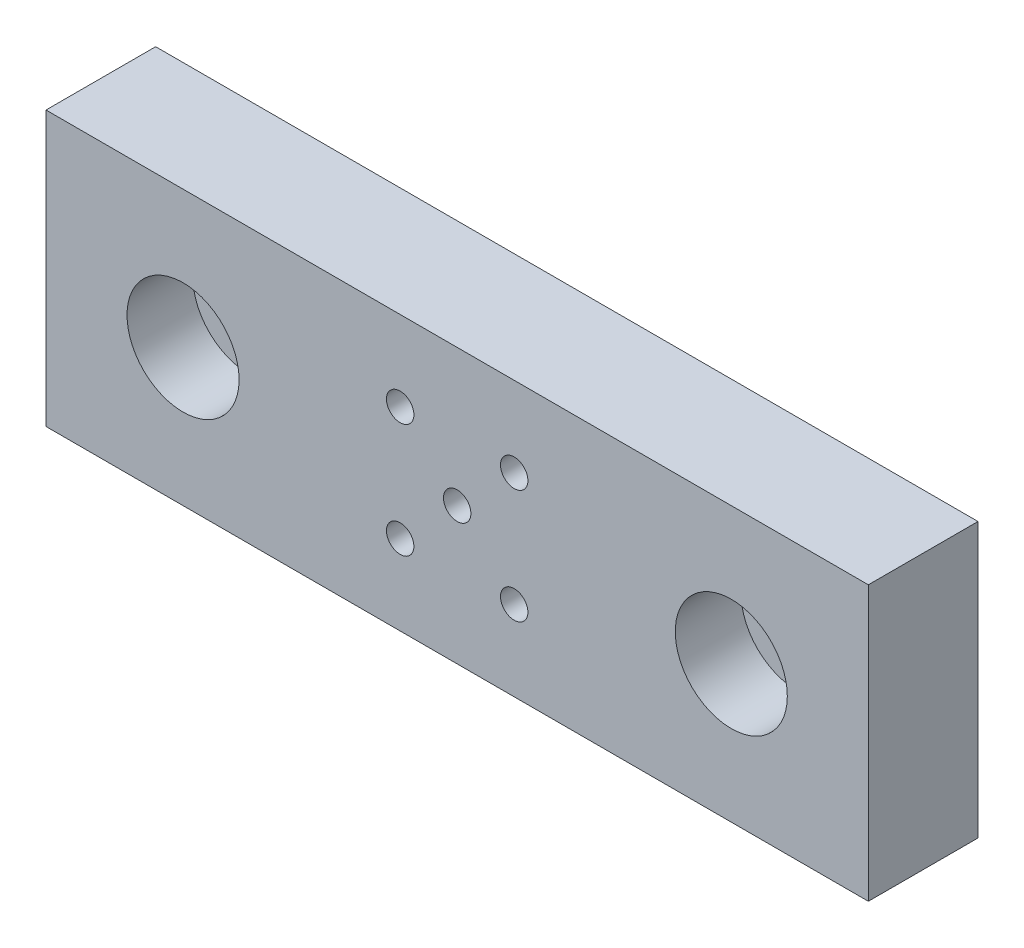
SolidWorks part; units mm, degrees
ref_plane "Front Plane" through (0, 0, 0) normal (0, 0, 1) x (1, 0, 0)
ref_plane "Top Plane" through (0, 0, 0) normal (0, 1, 0) x (1, 0, 0)
ref_plane "Right Plane" through (0, 0, 0) normal (1, 0, 0) x (0, 0, -1)
sketch "Sketch1" plane through (0, 0, 0) normal (0, 0, 1) x (1, 0, 0)
  line L0 (-48.6207, 0) -> (72.931, 0) construction
  line L1 (0, 34.4847) -> (0, -34.4847) construction
  line L2 (-37.5, 12.5) -> (37.5, 12.5)
  line L3 (-37.5, -12.5) -> (37.5, -12.5)
  line L4 (-37.5, 12.5) -> (-37.5, 0)
  line L5 (37.5, 12.5) -> (37.5, 0)
  line L10 (37.5, 0) -> (37.5, -12.5)
  line L11 (-37.5, 0) -> (-37.5, -12.5)
  circle A0 centre (-25, 0) radius 3.25
  circle A1 centre (25, 0) radius 3.25
  circle A4 centre (0, 0) radius 1.25
  circle A5 centre (-5.2, 5.2) radius 1.25
  circle A6 centre (5.2, 5.2) radius 1.25
  circle A7 centre (5.2, -5.2) radius 1.25
  circle A8 centre (-5.2, -5.2) radius 1.25
  dimension "D21" = 5.2
  dimension "D22" = 5.2
  dimension "D23" = 5.2
  dimension "D24" = 5.2
  dimension "D25" = 5.2
  dimension "D26" = 5.2
  dimension "D27" = 5.2
  dimension "D28" = 5.2
  dimension "D29" = 2.5
  dimension "D30" = 2.5
  dimension "D31" = 2.5
  dimension "D32" = 2.5
  dimension "D33" = 2.5
  dimension "D34" = 0
  dimension "D1" = 6.5
  dimension "D8" = 6.5
  dimension "D9" = 25
  dimension "D10" = 25
  dimension "D4" = 12.5
  dimension "D5" = 12.5
  dimension "D6" = 37.5
  dimension "D7" = 37.5
extrude "Boss-Extrude1" add sketch "Sketch1" along normal blind 10
cosmetic thread "Cosmetic Thread1" parameters "D2"=3
cosmetic thread "Cosmetic Thread2" parameters "D1"=5, "D2"=3
cosmetic thread "Cosmetic Thread3" parameters "D1"=5, "D2"=3
cosmetic thread "Cosmetic Thread4" parameters "D1"=5, "D2"=3
cosmetic thread "Cosmetic Thread5" parameters "D1"=5, "D2"=3
sketch "Sketch2" plane through (0, 0, 10) normal (0, 0, 1) x (1, 0, 0)
  circle A0 centre (-25, 0) radius 5.11
  circle A1 centre (25, 0) radius 5.11
  dimension "D1" = 10.22
  dimension "D2" = 10.22
extrude "Cut-Extrude1" cut sketch "Sketch2" against normal blind 6
